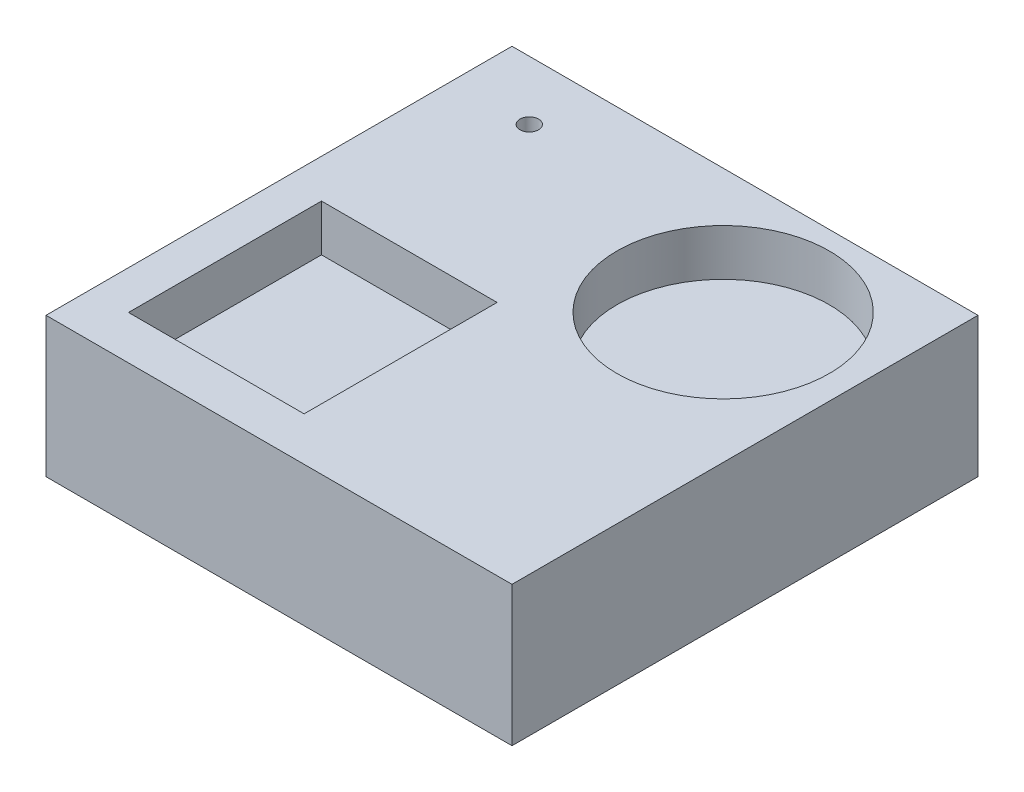
SolidWorks part; units mm, degrees
ref_plane "Front Plane" through (0, 0, 0) normal (0, 0, 1) x (1, 0, 0)
ref_plane "Top Plane" through (0, 0, 0) normal (0, 1, 0) x (1, 0, 0)
ref_plane "Right Plane" through (0, 0, 0) normal (1, 0, 0) x (0, 0, -1)
sketch "Sketch1" plane through (0, 0, 0) normal (0, 1, 0) x (1, 0, 0)
  line L1 (0, 0) -> (100, 0)
  line L2 (0, 0) -> (0, 100)
  line L3 (0, 100) -> (100, 100)
  line L4 (100, 0) -> (100, 100)
  dimension "D1" = 100
  dimension "D2" = 100
extrude "Boss-Extrude1" add sketch "Sketch1" along normal blind 30
sketch "Sketch5" plane through (0, 30, 0) normal (0, 1, 0) x (1, 0, 0)
  circle A0 centre (16.3843, 87.3232) radius 2
  dimension "D1" = 4
extrude "Cut-Extrude1" cut sketch "Sketch5" against normal through all
sketch "Sketch7" plane through (0, 30, 0) normal (0, 1, 0) x (1, 0, 0)
  line L1 (8.3279, 50.7874) -> (46.0114, 50.7874)
  line L2 (8.3279, 50.7874) -> (8.3279, 9.3741)
  line L3 (8.3279, 9.3741) -> (46.0114, 9.3741)
  line L4 (46.0114, 50.7874) -> (46.0114, 9.3741)
  circle A0 centre (72.0846, 73.2252) radius 22.79
  point P6 (72.0846, 73.2252)
  point P7 (0, 0)
  point P8 (50.2642, 9.3741)
  point P9 (0, 0)
  point P10 (0, 0)
  point P11 (46.0114, 50.7874)
extrude "Cut-Extrude2" cut sketch "Sketch7" against normal blind 10
